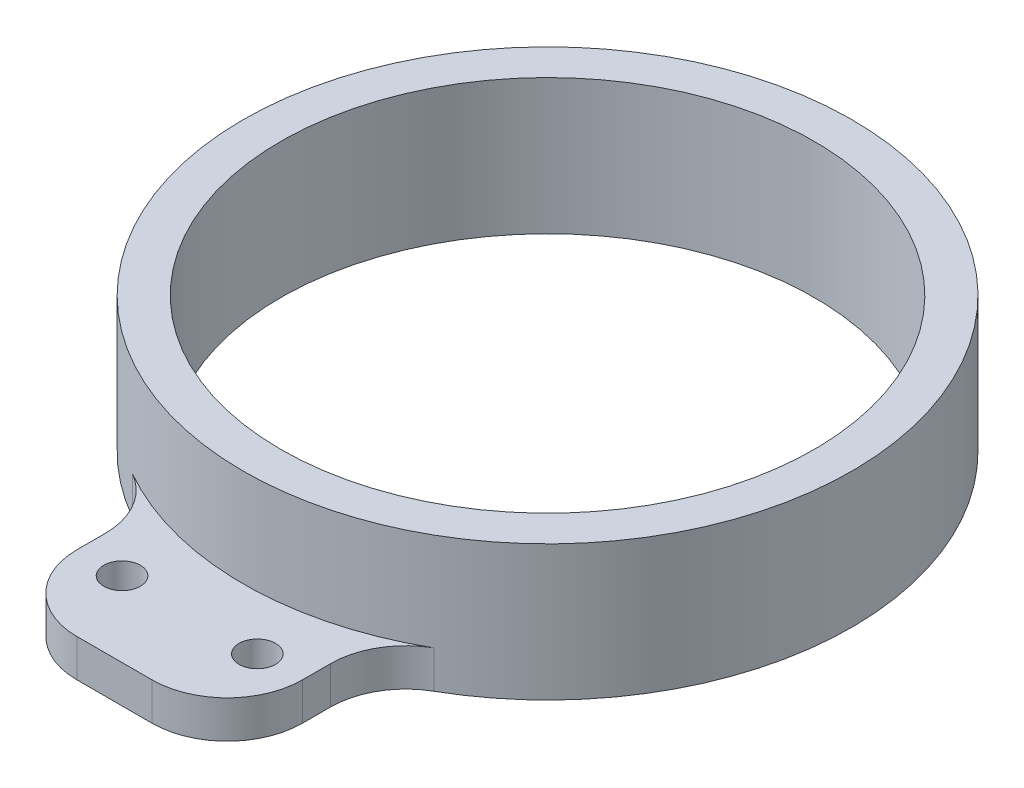
SolidWorks part; units mm, degrees
ref_plane "Alzado" through (0, 0, 0) normal (0, 0, 1) x (1, 0, 0)
ref_plane "Planta" through (0, 0, 0) normal (0, 1, 0) x (1, 0, 0)
ref_plane "Vista lateral" through (0, 0, 0) normal (1, 0, 0) x (0, 0, -1)
sketch "Croquis1" plane through (0, 0, 0) normal (0, 1, 0) x (1, 0, 0)
  circle A0 centre (0, 0) radius 35.5
  circle A1 centre (0, 0) radius 40.5
  dimension "D1" = 71
  dimension "D2" = 5
extrude "Saliente-Extruir1" add sketch "Croquis1" along normal mid plane 18
sketch "Croquis2" plane through (0, -9, 0) normal (0, -1, 0) x (1, 0, 0)
  line L0 (-15, 37.6198) -> (-15, 57.6198)
  line L1 (-15, 57.6198) -> (15, 57.6198)
  line L2 (15, 57.6198) -> (15, 37.6198)
  line L3 (0, 0) -> (0, 98.2113) construction
  circle A0 centre (0, 0) radius 40.5 construction
  arc A1 (15, 37.6198) -> (-15, 37.6198) centre (0, 0) ccw
  circle A2 centre (-9, 47.6198) radius 2.4293
  circle A3 centre (9, 47.6198) radius 2.4293
  point P7 (0, 57.6198)
  point P12 (-7.3189, 57.6198)
  dimension "D1" = 30
  dimension "D2" = 20
  dimension "D3" = 9
  dimension "D4" = 10
extrude "Saliente-Extruir2" add sketch "Croquis2" against normal blind 5
fillet "Redondeo1" radius 10 4 edges at (15, -6.5, 37.6198) (-15, -6.5, 37.6198) (-15, -6.5, 57.6198) (15, -6.5, 57.6198)
